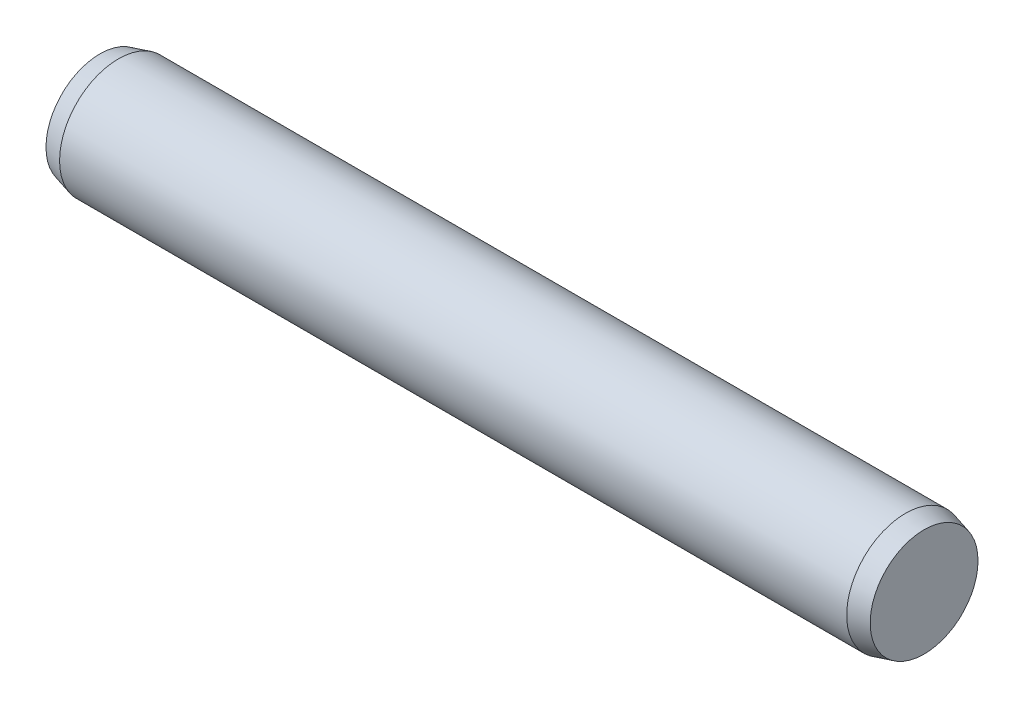
SolidWorks part; units mm, degrees
material "1.4310 (X10CrNi18-8)"
ref_plane "Front Plane" through (0, 0, 0) normal (0, 0, 1) x (1, 0, 0)
ref_plane "Top Plane" through (0, 0, 0) normal (0, 1, 0) x (1, 0, 0)
ref_plane "Right Plane" through (0, 0, 0) normal (1, 0, 0) x (0, 0, -1)
sketch "Sketch1" plane through (0, 0, 0) normal (0, 0, 1) x (1, 0, 0)
  line L0 (-13.37, 0) -> (13.37, 0) construction
  line L1 (13.37, 2) -> (13.37, -2) construction
  line L2 (-13.37, 2) -> (-13.37, -2) construction
  line L3 (14, 2) -> (14, -2) construction
  line L4 (-14, 2) -> (-14, -2) construction
  line L5 (-13.37, 0) -> (-14, 0) construction
  line L6 (13.37, 0) -> (14, 0) construction
  point P11 (10, 0)
  point P21 (-10, 0)
  dimension "Diameter" = 4
  dimension "Chamfer" = 0.63
  dimension "D1" = 0.63
  dimension "Length" = 28
  dimension "D2" = 4
  dimension "D3" = 4
sketch "Sketch2" plane through (0, 0, 0) normal (1, 0, 0) x (0, 0, -1)
  circle A0 centre (0, 0) radius 2
extrude "Extrude1" add sketch "Sketch2" against normal up to vertex (13.37 mm away) and the other way up to vertex (13.37 mm away) up to point (-13.37, 2, 0) other way up to point (13.37, 2, 0)
sketch "Sketch3" plane through (13.37, 0, 0) normal (1, 0, 0) x (0, 0, -1)
  circle A1 centre (0, 0) radius 2
  circle A2 centre (0, 0) radius 2
  dimension "D1" = 0
extrude "Extrude2" add sketch "Sketch3" along normal up to vertex (0.63 mm away) draft 15 up to point (14, 0, 0)
sketch "Sketch4" plane through (-13.37, 0, 0) normal (-1, 0, 0) x (0, 0, 1)
  circle A1 centre (0, 0) radius 2
  circle A2 centre (0, 0) radius 2
  dimension "D1" = 0
extrude "Extrude3" add sketch "Sketch4" along normal up to vertex (0.63 mm away) draft 15 up to point (-14, 0, 0)
sketch "Sketch5" plane through (0, 0, 0) normal (1, 0, 0) x (0, 0, -1)
  line L0 (-2, 0) -> (2, 0) construction
  point P4 (0, 0)
  dimension "D1" = 4
equation "\"D1@Sketch1\" = \"Chamfer@Sketch1\""
equation "\"D1@Sketch5\" = \"Diameter@Sketch1\""
equation "\"D2@Sketch1\" = \"Diameter@Sketch1\""
equation "\"D3@Sketch1\"=\"D2@Sketch1\""
